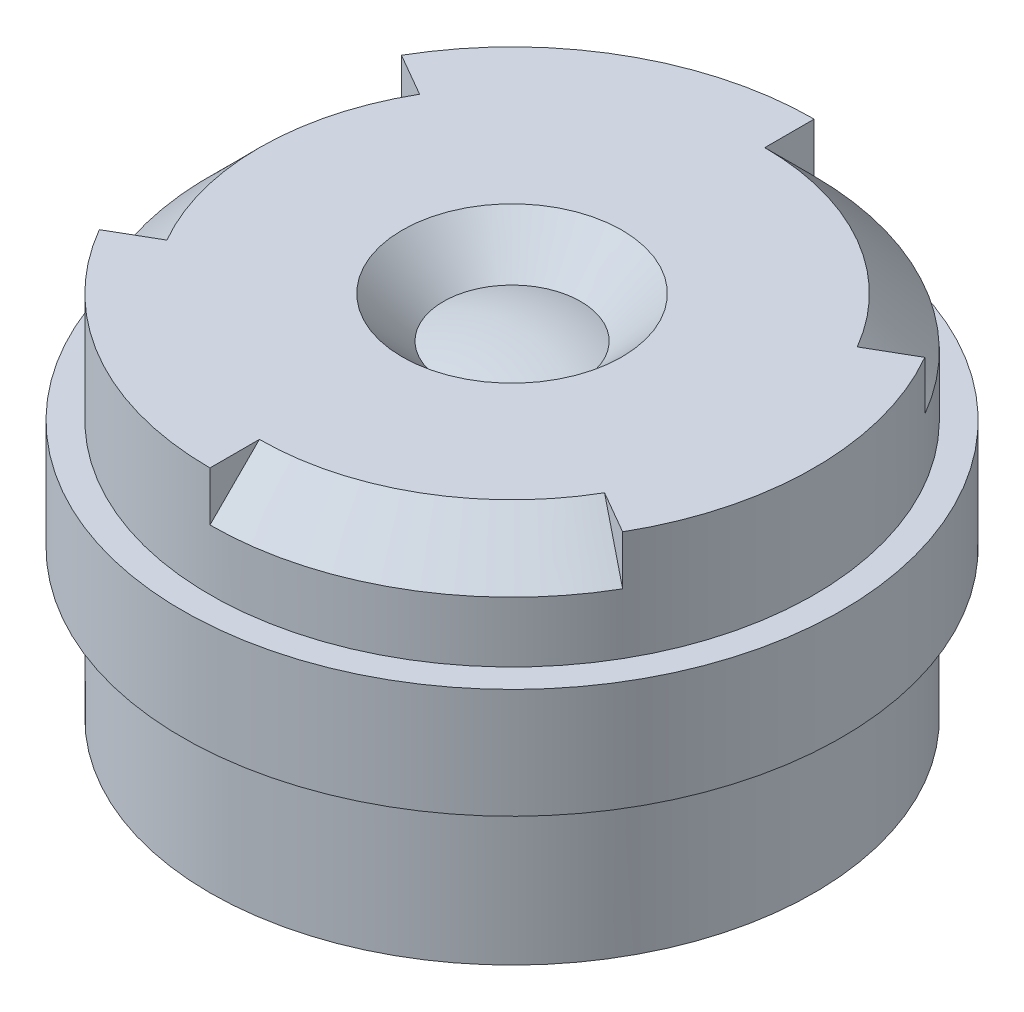
SolidWorks part; units mm, degrees
material "ABS PC"
ref_plane "Vorne" through (0, 0, 0) normal (0, 0, 1) x (1, 0, 0)
ref_plane "Oben" through (0, 0, 0) normal (0, 1, 0) x (1, 0, 0)
ref_plane "Rechts" through (0, 0, 0) normal (1, 0, 0) x (0, 0, -1)
sketch "Skizze3" plane through (0, 0, 0) normal (0, 0, 1) x (1, 0, 0)
  line L0 (0, 0) -> (0, -2.1568) construction
  line L1 (1, 0.8) -> (2.75, 0.8)
  line L2 (2.75, 0.8) -> (2.75, -2.55)
  line L3 (2.75, -2.55) -> (2.1, -2.55)
  line L4 (1, 0.8) -> (0.625, 0.425)
  line L5 (0.8125, 0.6125) -> (0.8125, 0.8) construction
  line L6 (0.8125, 0.8) -> (1, 0.8) construction
  line L7 (2.1, -2.55) -> (1.8, -2.25)
  line L8 (2.1, -2.55) -> (2.1, -2.4) construction
  line L9 (2.1, -2.4) -> (1.95, -2.4) construction
  line L10 (0, -2.55) -> (0, 0.525)
  arc A0 (1.8, -2.25) -> (0, -2.55) centre (0, 3) cw
  arc A1 (0, 0.525) -> (0.625, 0.425) centre (0, -1.4781) cw
revolve "Body" add sketch "Skizze3" angle 360 about L0
sketch "Skizze4" plane through (0, 0, 0) normal (0, 0, 1) x (1, 0, 0)
  line L0 (0, 0) -> (0, 1.3093) construction
  line L1 (2.75, -2.55) -> (2.75, 0.8) construction
  line L2 (2.75, -0.2) -> (3, -0.2)
  line L3 (2.75, -0.2) -> (2.75, -1.2)
  line L4 (2.75, -1.2) -> (3, -1.2)
  line L5 (3, -0.2) -> (3, -1.2)
  line L6 (2.75, 0.8) -> (-2.75, 0.8) construction
revolve "Thread" add sketch "Skizze4" angle 360 about L0
sketch "Skizze5" plane through (0, 0, 0) normal (1, 0, 0) x (0, 0, -1)
  line L0 (0, 0) -> (0, -3.7681) construction
  line L1 (2.75, 0.8) -> (2.75, 0.35)
  line L2 (2.75, -0.2) -> (2.75, 0.8) construction
  line L3 (2.75, 0.35) -> (2.3, 0.8)
  line L4 (2.75, 0.8) -> (-2.75, 0.8) construction
  line L5 (2.3, 0.8) -> (2.75, 0.8)
revolve "Toolface" cut sketch "Skizze5" angle 60 about L0
pattern_circular "Kreismuster1" count 3 over 360 about axis through (0, 0, 0) along (0, 1, 0) of "Toolface"
